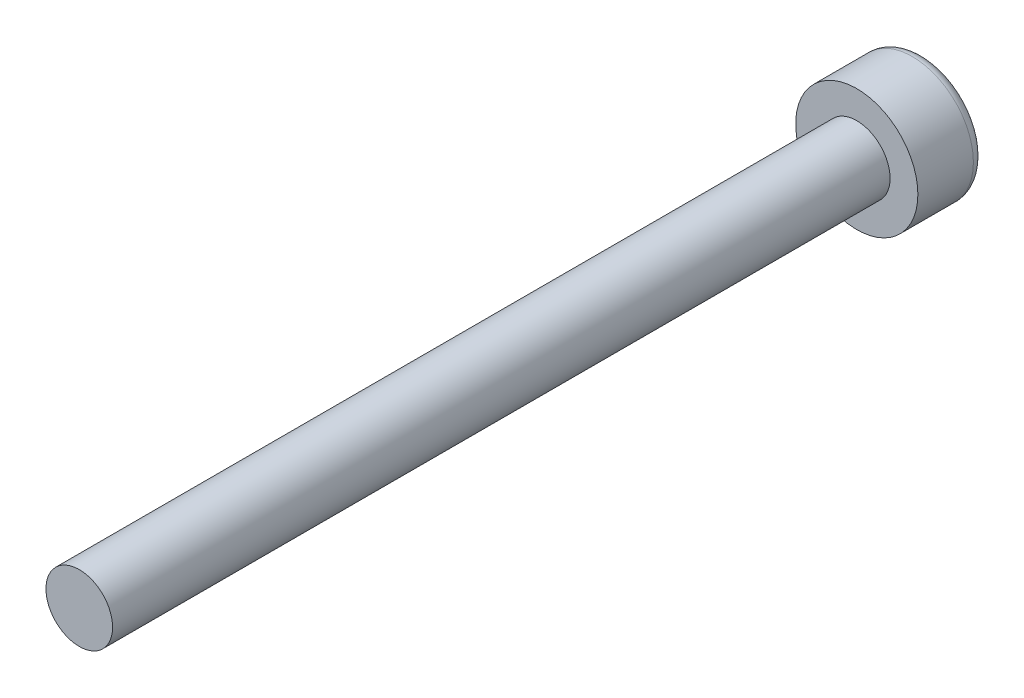
SolidWorks part; units mm, degrees
ref_plane "正面" through (0, 0, 0) normal (0, 0, 1) x (1, 0, 0)
ref_plane "平面" through (0, 0, 0) normal (0, 1, 0) x (1, 0, 0)
ref_plane "右側面" through (0, 0, 0) normal (1, 0, 0) x (0, 0, -1)
sketch "ｽｹｯﾁ2" plane through (0, 0, 0) normal (0, 0, 1) x (1, 0, 0)
  circle A0 centre (0, 0) radius 2.75
  dimension "D1" = 5.5
extrude "ﾎﾞｽ - 押し出し1" add sketch "ｽｹｯﾁ2" along normal blind 3
sketch "ｽｹｯﾁ3" plane through (0, 0, 3) normal (0, 0, 1) x (1, 0, 0)
  circle A0 centre (0, 0) radius 1.5
  dimension "D1" = 3
extrude "ﾎﾞｽ - 押し出し2" add sketch "ｽｹｯﾁ3" along normal blind 35
fillet "ﾌｨﾚｯﾄ1" radius 0.5 1 edges at (2.75, 0, 0)
